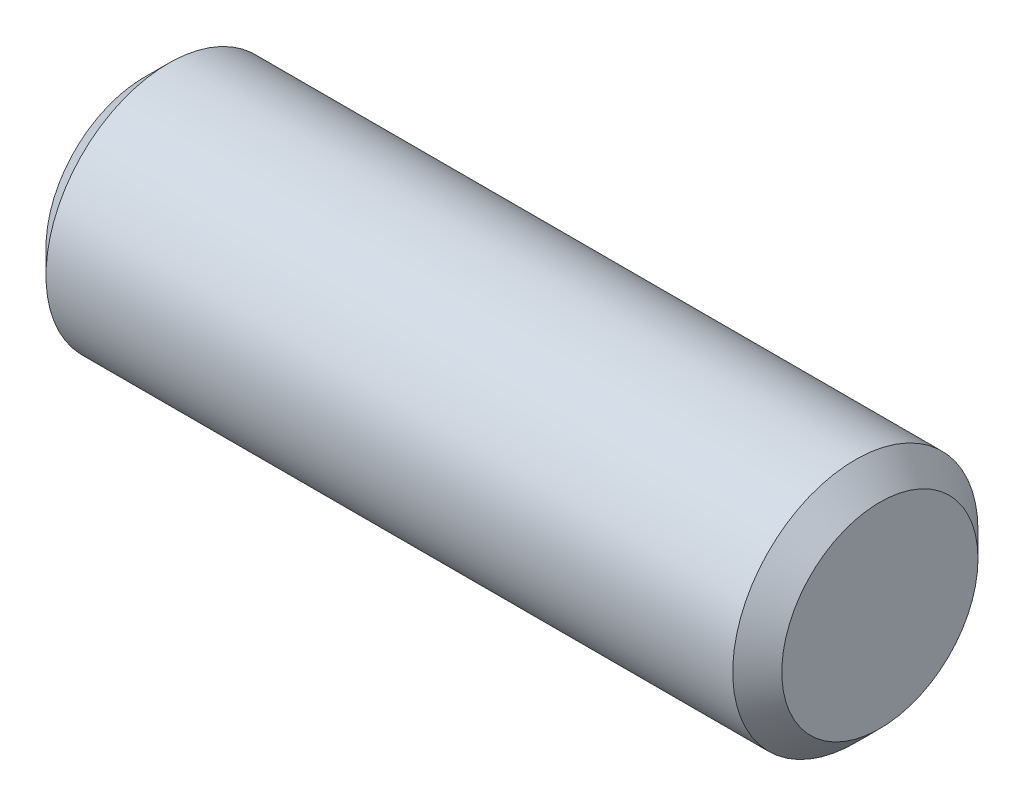
SolidWorks part; units mm, degrees
ref_plane "Front" through (0, 0, 0) normal (0, 0, 1) x (1, 0, 0)
ref_plane "Top" through (0, 0, 0) normal (0, 1, 0) x (1, 0, 0)
ref_plane "Right" through (0, 0, 0) normal (1, 0, 0) x (0, 0, -1)
sketch "Sketch1" plane through (0, 0, 0) normal (0, 0, 1) x (1, 0, 0)
  line L0 (-9.525, 0) -> (9.525, 0) construction
  line L1 (9.525, 3.175) -> (9.525, -3.175) construction
  line L2 (-9.525, 3.175) -> (-9.525, -3.175) construction
  dimension "Length" = 19.05
  dimension "Diameter" = 6.35
sketch "Sketch2" plane through (0, 0, 0) normal (1, 0, 0) x (0, 0, -1)
  circle A0 centre (0, 0) radius 3.175
extrude "Extrude1" add sketch "Sketch2" against normal up to vertex (9.525 mm away) and the other way up to vertex (9.525 mm away) up to point (-9.525, 3.175, 0) other way up to point (9.525, 3.175, 0)
chamfer "Chamfer1" distance 0.635 angle 45 2 edges at (9.525, 0, -3.175) (-9.525, 0, -3.175)
equation "\"D1@Chamfer1\" = \"Diameter@Sketch1\"*.1"
